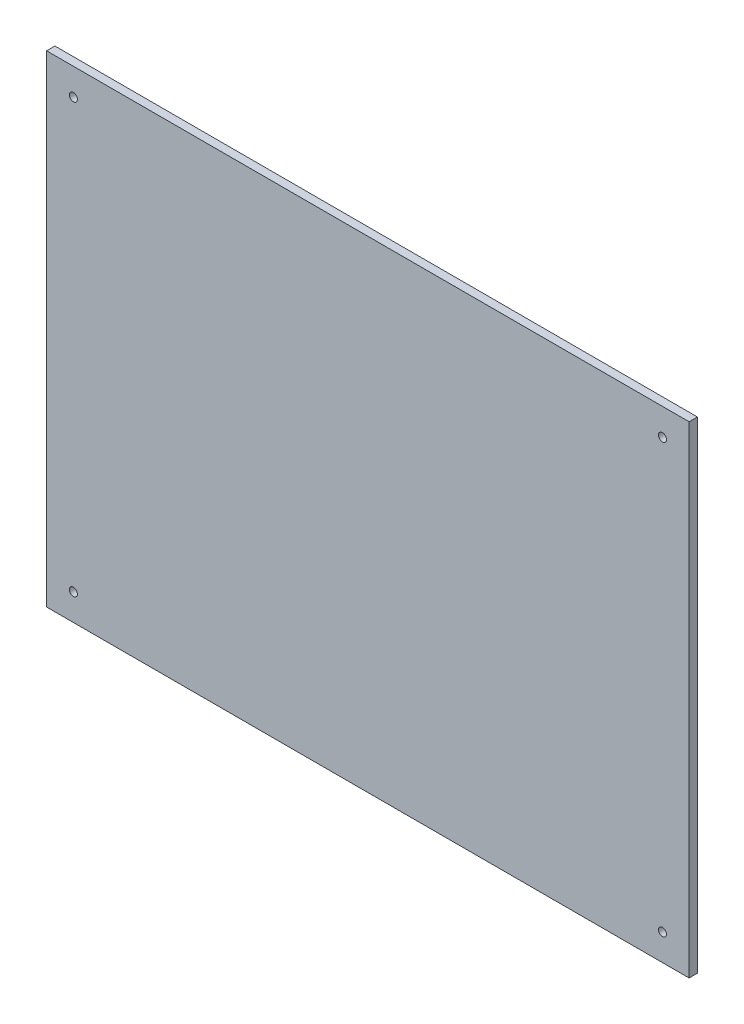
SolidWorks part; units mm, degrees
ref_plane "Front Plane" through (0, 0, 0) normal (0, 0, 1) x (1, 0, 0)
ref_plane "Top Plane" through (0, 0, 0) normal (0, 1, 0) x (1, 0, 0)
ref_plane "Right Plane" through (0, 0, 0) normal (1, 0, 0) x (0, 0, -1)
sketch "Sketch1" plane through (0, 0, 0) normal (0, 0, 1) x (1, 0, 0)
  line L1 (60.95, -45.7) -> (-60.95, -45.7)
  line L2 (60.95, -45.7) -> (60.95, 45.7)
  line L3 (60.95, 45.7) -> (-60.95, 45.7)
  line L4 (-60.95, -45.7) -> (-60.95, 45.7)
  line L5 (60.95, -45.7) -> (-60.95, 45.7) construction
  line L6 (60.95, 45.7) -> (-60.95, -45.7) construction
  circle A0 centre (-55.87, 40.62) radius 0.762
  circle A1 centre (55.89, 40.62) radius 0.762
  circle A2 centre (55.89, -40.66) radius 0.762
  circle A3 centre (-55.87, -40.66) radius 0.762
  point P0 (0, 0)
  dimension "D3" = 1.524
  dimension "D1" = 121.9
  dimension "D2" = 91.4
  dimension "D4" = 5.08
  dimension "D5" = 5.08
  dimension "D6" = 2
  dimension "D7" = 2
extrude "Boss-Extrude1" add sketch "Sketch1" along normal blind 1.5748
